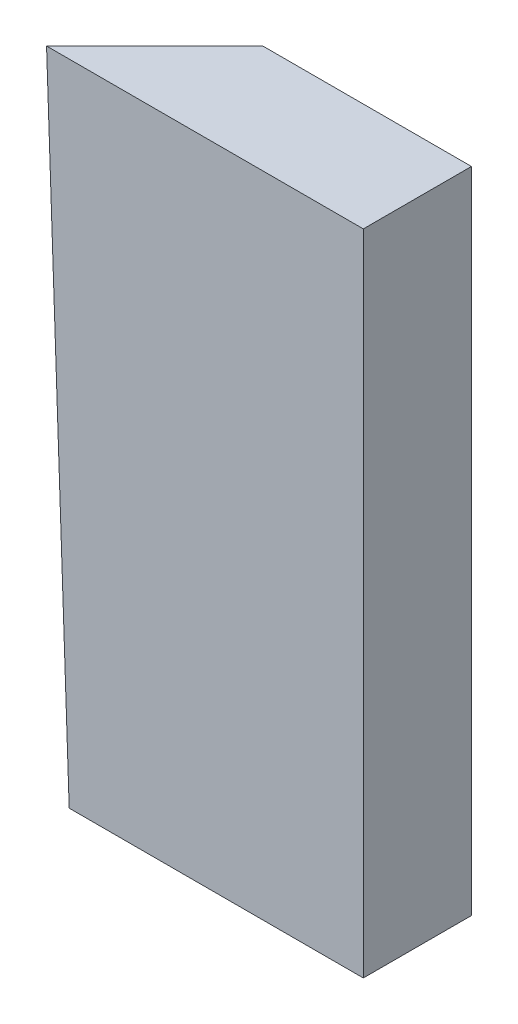
SolidWorks part; units mm, degrees
ref_plane "Alzado" through (0, 0, 0) normal (0, 0, 1) x (1, 0, 0)
ref_plane "Planta" through (0, 0, 0) normal (0, 1, 0) x (1, 0, 0)
ref_plane "Vista lateral" through (0, 0, 0) normal (1, 0, 0) x (0, 0, -1)
sketch "Croquis5" plane through (0, 0, 0) normal (0, 1, 0) x (1, 0, 0)
  line L0 (0, 0) -> (34, 0)
  line L1 (34, 0) -> (34, 12.5)
  line L2 (34, 12.5) -> (12.5, 12.5)
  line L3 (12.5, 12.5) -> (0, 0)
  dimension "D1" = 34
  dimension "D2" = 12.5
  dimension "D3" = 21.5
sketch "Croquis6" plane through (0, 0, 0) normal (0, 0, 1) x (1, 0, 0)
  line L0 (0, 0) -> (-2.6191, 75)
  line L2 (0, 75) -> (0, 0) construction
  dimension "D1" = 75
  dimension "D2" = 75
  dimension "D3" = 2
ref_plane "Plano2" through (0, 75, 0) normal (0, 1, 0) x (1, 0, 0)
sketch "Croquis7" plane through (0, 75, 0) normal (0, 1, 0) x (1, 0, 0)
  line L0 (34.0009, 0) -> (34.0009, 12.5)
  line L1 (34.0009, 12.5) -> (9.8809, 12.5)
  line L2 (9.8809, 12.5) -> (-2.6191, 0)
  line L3 (-2.6191, 0) -> (34.0009, 0)
  point P0 (0, 0)
  dimension "D1" = 12.5
  dimension "D2" = 36.62
  dimension "D3" = 24.12
  dimension "D4" = 17.6777
loft "Recubrir3" add profiles "Croquis7", "Croquis5"
